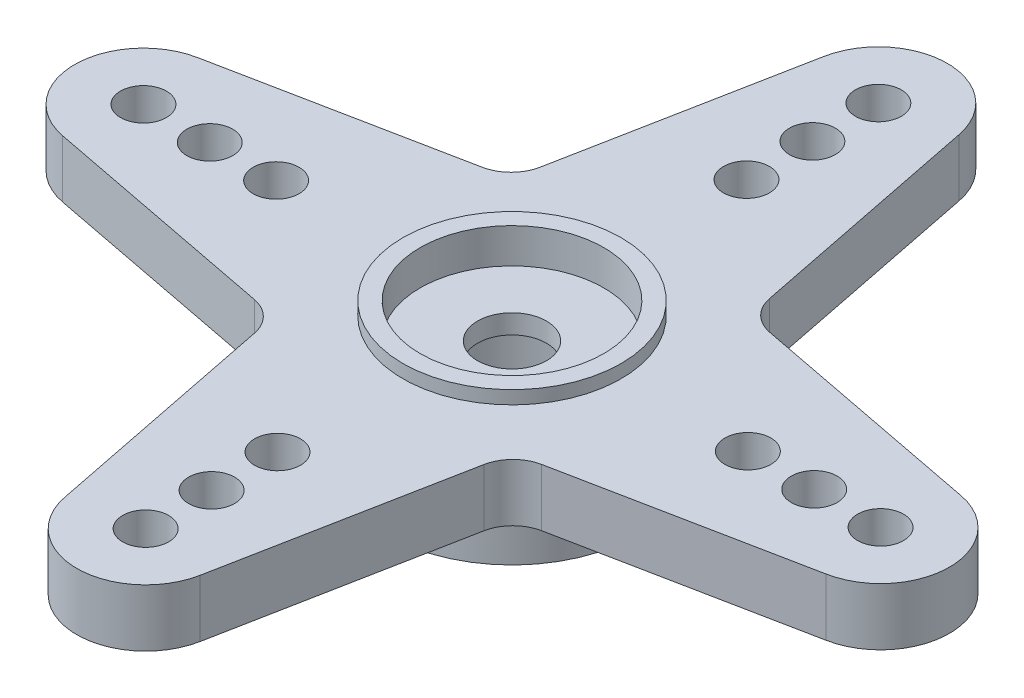
SolidWorks part; units mm, degrees
ref_plane "Front Plane" through (0, 0, 0) normal (0, 0, 1) x (1, 0, 0)
ref_plane "Top Plane" through (0, 0, 0) normal (0, 1, 0) x (1, 0, 0)
ref_plane "Right Plane" through (0, 0, 0) normal (1, 0, 0) x (0, 0, -1)
sketch "Sketch1" plane through (0, 0, 0) normal (0, 1, 0) x (1, 0, 0)
  line L0 (-999.9955, -2.9887) -> (48999.7812, 146.4466) construction
  line L1 (2.9887, -999.9955) -> (-146.4466, 48999.7812) construction
  line L2 (-3.9634, 4.9382) -> (-2.3759, 13.1518)
  line L3 (3.9338, 4.9618) -> (2.3, 13.1518)
  line L4 (4.9382, 3.9634) -> (13.1518, 2.3759)
  line L5 (4.9618, -3.9338) -> (13.1518, -2.3)
  line L6 (3.9634, -4.9382) -> (2.3759, -13.1518)
  line L7 (-3.9338, -4.9618) -> (-2.3, -13.1518)
  line L8 (-4.1252, 4.1006) -> (-4.1006, -4.1252) construction
  line L9 (-4.1252, 4.1006) -> (4.1006, 4.1252) construction
  line L10 (-4.1006, -4.1252) -> (4.1252, -4.1006) construction
  line L11 (4.1006, 4.1252) -> (4.1252, -4.1006) construction
  line L12 (-4.9382, -3.9634) -> (-13.1518, -2.3759)
  line L13 (-4.9618, 3.9338) -> (-13.1518, 2.3)
  circle A0 centre (0, 0) radius 1.1906
  circle A1 centre (0, 0) radius 5.8166 construction
  arc A2 (-2.3759, 13.1518) -> (2.3, 13.1518) centre (-0.038, 12.6999) cw
  circle A3 centre (-0.038, 12.6999) radius 0.7937
  circle A4 centre (-0.0311, 10.414) radius 0.7937
  circle A5 centre (-0.0243, 8.128) radius 0.7937
  arc A6 (13.1518, 2.3759) -> (13.1518, -2.3) centre (12.6999, 0.038) cw
  circle A7 centre (12.6999, 0.038) radius 0.7937
  circle A8 centre (10.414, 0.0311) radius 0.7937
  circle A9 centre (8.128, 0.0243) radius 0.7938
  arc A10 (2.3759, -13.1518) -> (-2.3, -13.1518) centre (0.038, -12.6999) cw
  circle A11 centre (0.038, -12.6999) radius 0.7937
  circle A12 centre (0.0311, -10.414) radius 0.7938
  circle A13 centre (0.0243, -8.128) radius 0.7938
  arc A14 (-13.1518, -2.3759) -> (-13.1518, 2.3) centre (-12.6999, -0.038) cw
  circle A15 centre (-12.6999, -0.038) radius 0.7937
  circle A16 centre (-10.414, -0.0311) radius 0.7937
  circle A17 centre (-8.128, -0.0243) radius 0.7937
  arc A18 (3.9338, 4.9618) -> (4.9382, 3.9634) centre (5.1792, 5.2103) ccw
  arc A19 (-3.9338, -4.9618) -> (-4.9382, -3.9634) centre (-5.1792, -5.2103) ccw
  arc A20 (-3.9634, 4.9382) -> (-4.9618, 3.9338) centre (-5.2103, 5.1792) cw
  arc A21 (3.9634, -4.9382) -> (4.9618, -3.9338) centre (5.2103, -5.1792) cw
  point P56 (4.1129, 0.0123)
  point P57 (-4.1129, -0.0123)
  dimension "D1" = 11.6332
  dimension "D2" = 2.3813
  dimension "D3" = 2.3813
  dimension "D5" = 1.5875
  dimension "D8" = 1.27
  dimension "D9" = 1.27
  dimension "D10" = 1.27
  dimension "D11" = 1.27
  dimension "D4" = 12.7
  dimension "D6" = 3
  dimension "D7" = 4
extrude "Boss-Extrude1" add sketch "Sketch1" along normal blind 1.9844
sketch "Sketch2" plane through (0, 1.9844, 0) normal (0, 1, 0) x (1, 0, 0)
  circle A0 centre (0, 0) radius 3.175
  dimension "D1" = 6.35
extrude "Cut-Extrude1" cut sketch "Sketch2" against normal blind 0.7493
sketch "Sketch3" plane through (0, 0, 0) normal (0, -1, 0) x (1, 0, 0)
  circle A0 centre (0, 0) radius 4.3656
  dimension "D1" = 8.7312
extrude "Boss-Extrude2" add sketch "Sketch3" along normal blind 2.3876
sketch "Sketch4" plane through (0, -2.3876, 0) normal (0, -1, 0) x (1, 0, 0)
  circle A0 centre (0, 0) radius 2.7781
  dimension "D1" = 5.5562
extrude "Cut-Extrude2" cut sketch "Sketch4" against normal blind 2.9591
sketch "Sketch5" plane through (0, 1.9844, 0) normal (0, 1, 0) x (1, 0, 0)
  circle A0 centre (0, 0) radius 3.175
  circle A1 centre (0, 0) radius 3.7703
  dimension "D1" = 7.5406
extrude "Boss-Extrude3" add sketch "Sketch5" along normal blind 0.4572
